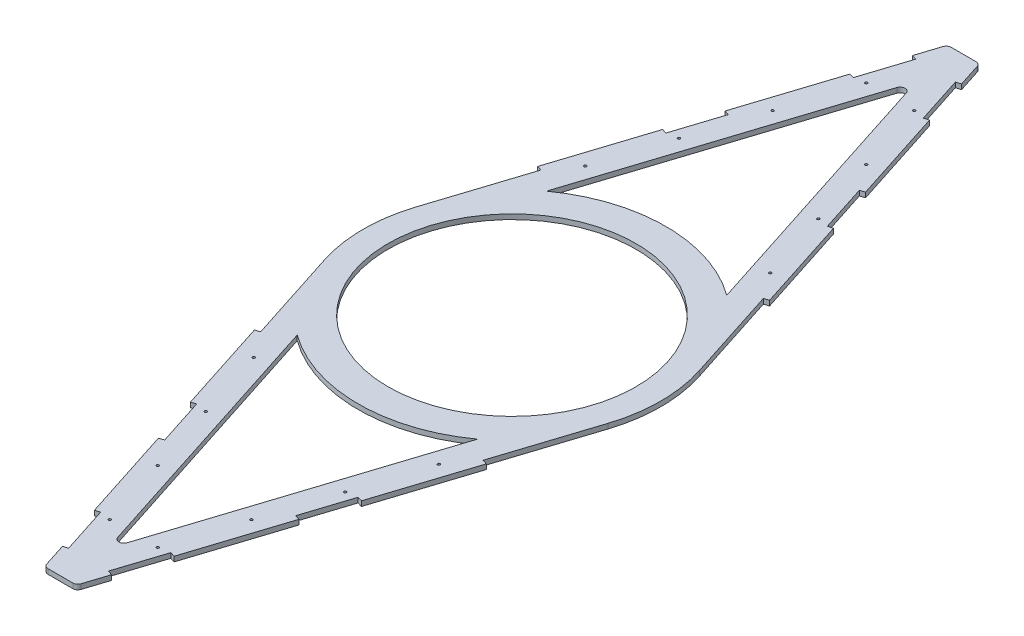
SolidWorks part; units mm, degrees
ref_plane "Front Plane" through (0, 0, 0) normal (0, 0, 1) x (1, 0, 0)
ref_plane "Top Plane" through (0, 0, 0) normal (0, 1, 0) x (1, 0, 0)
ref_plane "Right Plane" through (0, 0, 0) normal (1, 0, 0) x (0, 0, -1)
sketch "Sketch2" plane through (0, 0, 0) normal (0, 1, 0) x (1, 0, 0)
  line L0 (-295.0403, 95.1378) -> (-34.5174, 903.069)
  line L1 (-25, 910) -> (25, 910)
  line L2 (0, 0) -> (0, 979.251) construction
  line L3 (-181.6808, 251.1814) -> (-9.5174, 785.0928)
  line L4 (295.0403, 95.1378) -> (32.2825, 910)
  line L5 (181.6808, 251.1814) -> (9.5174, 785.0928)
  line L6 (0, 912.3611) -> (-253.9796, 124.7221) construction
  line L7 (0, 912.3611) -> (253.9796, 124.7221) construction
  line L8 (-591.5307, 0) -> (570.3863, 0) construction
  line L9 (181.6808, -251.1814) -> (9.5174, -785.0928)
  line L10 (295.0403, -95.1378) -> (32.2825, -910)
  line L11 (-181.6808, -251.1814) -> (-9.5174, -785.0928)
  line L12 (-25, -910) -> (25, -910)
  line L13 (-295.0403, -95.1378) -> (-34.5174, -903.069)
  circle A0 centre (0, 0) radius 250
  arc A1 (181.6808, 251.1814) -> (-181.6808, 251.1814) centre (0, 0) ccw
  arc A2 (-9.5174, 785.0928) -> (9.5174, 785.0928) centre (0, 782.0238) cw
  arc A3 (-295.0403, 95.1378) -> (-295.0403, -95.1378) centre (0, 0) ccw
  arc A4 (-25, 910) -> (-34.5174, 903.069) centre (-25, 900) ccw
  arc A5 (25, 910) -> (34.5174, 903.069) centre (25, 900) cw
  circle A6 centre (-186.4767, 334.0614) radius 2.5
  circle A7 centre (-140.4423, 476.8229) radius 2.5
  circle A8 centre (-94.4079, 619.5843) radius 2.5
  circle A9 centre (-48.3735, 762.3458) radius 2.5
  circle A10 centre (48.3735, 762.3458) radius 2.5
  circle A11 centre (94.4079, 619.5843) radius 2.5
  circle A12 centre (140.4423, 476.8229) radius 2.5
  circle A13 centre (186.4767, 334.0614) radius 2.5
  circle A14 centre (186.4767, -334.0614) radius 2.5
  circle A15 centre (140.4423, -476.8229) radius 2.5
  circle A16 centre (94.4079, -619.5843) radius 2.5
  circle A17 centre (48.3735, -762.3458) radius 2.5
  circle A18 centre (-48.3735, -762.3458) radius 2.5
  circle A19 centre (-94.4079, -619.5843) radius 2.5
  circle A20 centre (-140.4423, -476.8229) radius 2.5
  circle A21 centre (-186.4767, -334.0614) radius 2.5
  arc A22 (25, -910) -> (34.5174, -903.069) centre (25, -900) ccw
  arc A23 (-25, -910) -> (-34.5174, -903.069) centre (-25, -900) cw
  arc A24 (-9.5174, -785.0928) -> (9.5174, -785.0928) centre (0, -782.0238) ccw
  arc A25 (181.6808, -251.1814) -> (-181.6808, -251.1814) centre (0, 0) cw
  arc A26 (-181.6808, -251.1814) -> (181.6808, -251.1814) centre (0, 0) ccw
  arc A27 (295.0403, -95.1378) -> (295.0403, 95.1378) centre (0, 0) ccw
  point P15 (0, 814.6081)
  point P17 (-32.2825, 910)
  point P21 (0, 910)
  point P69 (0, -910)
  dimension "D1" = 500
  dimension "D2" = 10
  dimension "D3" = 10
  dimension "D4" = 5
  dimension "D5" = 150
  dimension "D6" = 150
  dimension "D7" = 150
  dimension "D8" = 60
  dimension "D9" = 910
  dimension "D11" = 50
  dimension "D12" = 30
extrude "Boss-Extrude1" add sketch "Sketch2" along normal blind 10 contours A5 L1 A4 L0 A3 L4 A12 A10 A9 A8 A7 A6 A0 L3 A2 L5 A1 A11 A13
sketch "Sketch3" plane through (0, 10, 0) normal (0, 1, 0) x (1, 0, 0)
  line L0 (-49.5235, -856.5322) -> (-40.0061, -853.4632)
  line L1 (-295.0403, -95.1378) -> (-34.5174, -903.069) construction
  line L2 (-40.0061, -853.4632) -> (-285.5229, -92.0688) construction
  line L3 (-49.5235, -856.5322) -> (-80.2131, -761.3579)
  line L4 (-49.5235, -856.5322) -> (-295.0403, -95.1378) construction
  line L5 (-70.6957, -758.2889) -> (-80.2131, -761.3579)
  line L6 (-132.0749, -567.9403) -> (-141.5923, -571.0093)
  line L7 (-162.7645, -472.766) -> (-172.2819, -475.835)
  line L8 (0, 1168.7659) -> (0, -1304.5967) construction
  line L9 (-233.6611, -285.4864) -> (-224.1437, -282.4174)
  line L12 (-587.2618, 0) -> (538.7715, 0) construction
  line L13 (-49.5235, 856.5322) -> (-295.0403, 95.1378) construction
  line L14 (-141.5923, -571.0093) -> (-172.2819, -475.835)
  line L15 (-70.6957, -758.2889) -> (-40.0061, -853.4632)
  line L16 (-162.7645, -472.766) -> (-132.0749, -567.9403)
  line L17 (-285.5229, -92.0688) -> (-224.1437, -282.4174)
  line L18 (-295.0403, -95.1378) -> (-233.6611, -285.4864)
  line L19 (-40.0061, 853.4632) -> (-285.5229, 92.0688) construction
  line L20 (-49.5235, 856.5322) -> (-40.0061, 853.4632)
  line L21 (-295.0403, 95.1378) -> (-233.6611, 285.4864)
  line L22 (-285.5229, 92.0688) -> (-224.1437, 282.4174)
  line L23 (-162.7645, 472.766) -> (-132.0749, 567.9403)
  line L24 (-70.6957, 758.2889) -> (-40.0061, 853.4632)
  line L25 (-141.5923, 571.0093) -> (-172.2819, 475.835)
  line L28 (-233.6611, 285.4864) -> (-224.1437, 282.4174)
  line L29 (-162.7645, 472.766) -> (-172.2819, 475.835)
  line L30 (-132.0749, 567.9403) -> (-141.5923, 571.0093)
  line L31 (-70.6957, 758.2889) -> (-80.2131, 761.3579)
  line L32 (-49.5235, 856.5322) -> (-80.2131, 761.3579)
  line L33 (49.5235, 856.5322) -> (40.0061, 853.4632)
  line L34 (40.0061, 853.4632) -> (285.5229, 92.0688) construction
  line L35 (49.5235, 856.5322) -> (295.0403, 95.1378) construction
  line L36 (0, -1168.7659) -> (0, 1304.5967) construction
  line L37 (49.5235, -856.5322) -> (295.0403, -95.1378) construction
  line L38 (40.0061, -853.4632) -> (285.5229, -92.0688) construction
  line L39 (49.5235, -856.5322) -> (40.0061, -853.4632)
  line L40 (49.5235, 856.5322) -> (80.2131, 761.3579)
  line L41 (70.6957, 758.2889) -> (80.2131, 761.3579)
  line L42 (132.0749, 567.9403) -> (141.5923, 571.0093)
  line L43 (162.7645, 472.766) -> (172.2819, 475.835)
  line L44 (233.6611, 285.4864) -> (224.1437, 282.4174)
  line L47 (141.5923, 571.0093) -> (172.2819, 475.835)
  line L48 (70.6957, 758.2889) -> (40.0061, 853.4632)
  line L49 (162.7645, 472.766) -> (132.0749, 567.9403)
  line L50 (285.5229, 92.0688) -> (224.1437, 282.4174)
  line L51 (295.0403, 95.1378) -> (233.6611, 285.4864)
  line L52 (295.0403, -95.1378) -> (233.6611, -285.4864)
  line L53 (285.5229, -92.0688) -> (224.1437, -282.4174)
  line L54 (162.7645, -472.766) -> (132.0749, -567.9403)
  line L55 (70.6957, -758.2889) -> (40.0061, -853.4632)
  line L56 (141.5923, -571.0093) -> (172.2819, -475.835)
  line L59 (233.6611, -285.4864) -> (224.1437, -282.4174)
  line L60 (162.7645, -472.766) -> (172.2819, -475.835)
  line L61 (132.0749, -567.9403) -> (141.5923, -571.0093)
  line L62 (70.6957, -758.2889) -> (80.2131, -761.3579)
  line L63 (49.5235, -856.5322) -> (80.2131, -761.3579)
  arc A0 (-285.5229, 92.0688) -> (-285.5229, -92.0688) centre (0, 0) ccw construction
  arc A1 (-295.0403, 95.1378) -> (-295.0403, -95.1378) centre (0, 0) ccw construction
  arc A3 (-285.5229, 92.0688) -> (-285.5229, -92.0688) centre (0, 0) ccw
  arc A4 (-295.0403, 95.1378) -> (-295.0403, -95.1378) centre (0, 0) ccw
  arc A5 (295.0403, 95.1378) -> (295.0403, -95.1378) centre (0, 0) cw construction
  arc A6 (285.5229, 92.0688) -> (285.5229, -92.0688) centre (0, 0) cw construction
  arc A7 (295.0403, 95.1378) -> (295.0403, -95.1378) centre (0, 0) cw
  arc A8 (285.5229, 92.0688) -> (285.5229, -92.0688) centre (0, 0) cw
  dimension "D1" = 10
  dimension "D2" = 800
  dimension "D3" = 100
  dimension "D4" = 200
  dimension "D5" = 100
  dimension "D6" = 200
extrude "Cut-Extrude1" cut sketch "Sketch3" against normal through all
